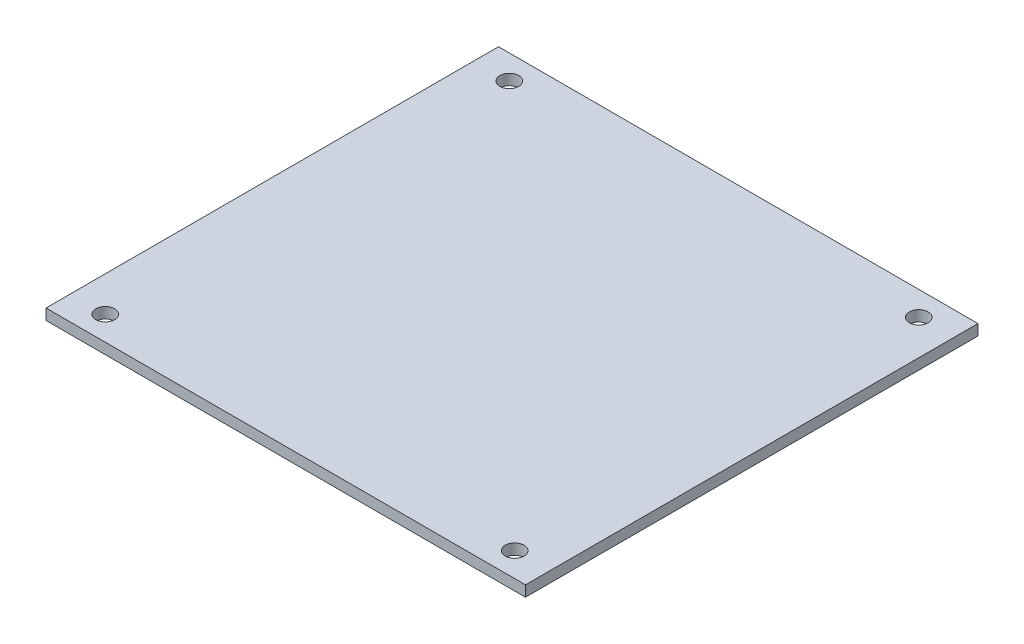
SolidWorks part; units mm, degrees
ref_plane "Front Plane" through (0, 0, 0) normal (0, 0, 1) x (1, 0, 0)
ref_plane "Top Plane" through (0, 0, 0) normal (0, 1, 0) x (1, 0, 0)
ref_plane "Right Plane" through (0, 0, 0) normal (1, 0, 0) x (0, 0, -1)
sketch "Sketch1" plane through (0, 0, 0) normal (0, 1, 0) x (1, 0, 0)
  line L1 (44.5, 42) -> (-44.5, 42)
  line L2 (44.5, 42) -> (44.5, -42)
  line L3 (44.5, -42) -> (-44.5, -42)
  line L4 (-44.5, 42) -> (-44.5, -42)
  line L5 (44.5, 42) -> (-44.5, -42) construction
  line L6 (44.5, -42) -> (-44.5, 42) construction
  point P0 (0, 0)
  dimension "D1" = 89
  dimension "D2" = 84
extrude "Boss-Extrude1" add sketch "Sketch1" along normal blind 2
sketch "Sketch2" plane through (0, 0, 0) normal (0, -1, 0) x (1, 0, 0)
  line L1 (38, 37.5) -> (-38, 37.5) construction
  line L2 (38, 37.5) -> (38, -37.5) construction
  line L3 (38, -37.5) -> (-38, -37.5) construction
  line L4 (-38, 37.5) -> (-38, -37.5) construction
  line L5 (38, 37.5) -> (-38, -37.5) construction
  line L6 (38, -37.5) -> (-38, 37.5) construction
  circle A0 centre (-38, 37.5) radius 1.75
  circle A1 centre (-38, -37.5) radius 1.75
  circle A2 centre (38, -37.5) radius 1.75
  circle A3 centre (38, 37.5) radius 1.75
  point P0 (0, 0)
  dimension "D3" = 3.5
  dimension "D1" = 76
  dimension "D2" = 75
extrude "Cut-Extrude1" cut sketch "Sketch2" against normal blind 10 contours A0 | A3 | A2 | A1
